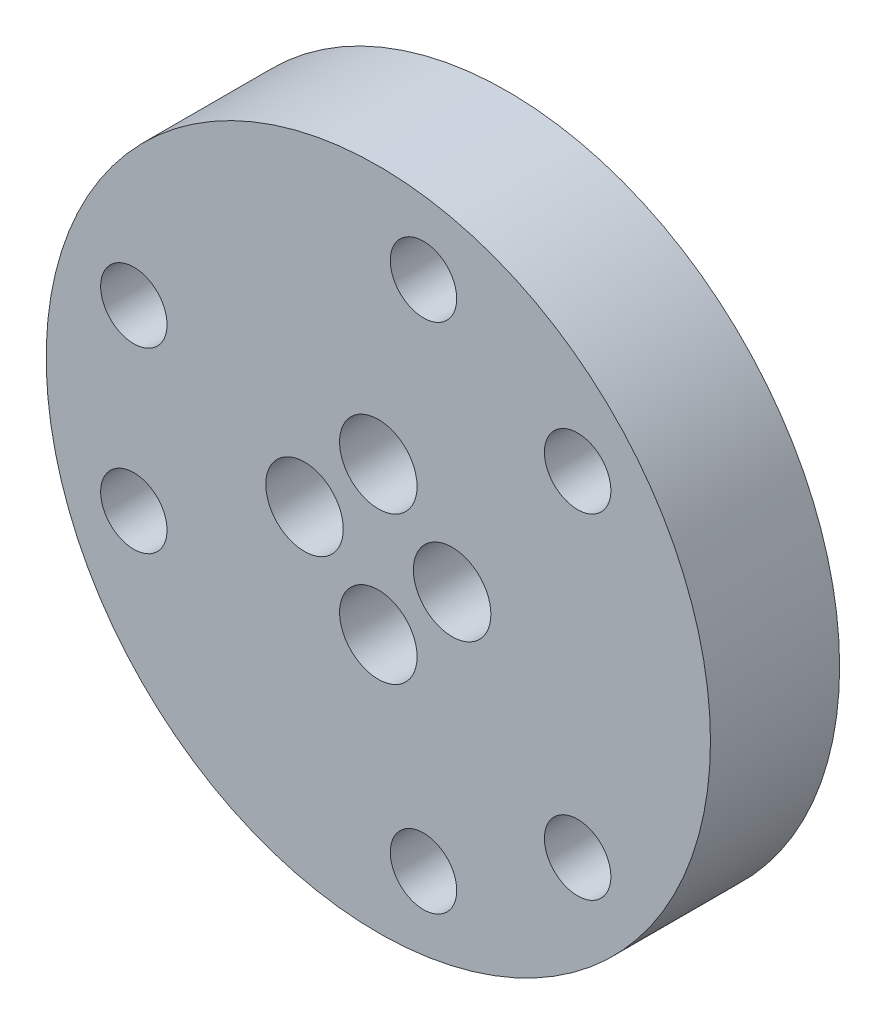
SolidWorks part; units mm, degrees
ref_plane "정면" through (0, 0, 0) normal (0, 0, 1) x (1, 0, 0)
ref_plane "윗면" through (0, 0, 0) normal (0, 1, 0) x (1, 0, 0)
ref_plane "우측면" through (0, 0, 0) normal (1, 0, 0) x (0, 0, -1)
sketch "스케치1" plane through (0, 0, 0) normal (0, 0, 1) x (1, 0, 0)
  line L0 (0, 0) -> (-14.1, 0) construction
  line L1 (0, 0) -> (-13.2497, 4.8225) construction
  circle A0 centre (0, 0) radius 18
  circle A1 centre (0, 4) radius 1.1
  circle A2 centre (4, 0) radius 1.1
  circle A3 centre (0, -4) radius 1.1
  circle A4 centre (-4, 0) radius 1.1
  circle A5 centre (0, 0) radius 14.1 construction
  circle A6 centre (-13.2497, 4.8225) radius 1.6
  circle A7 centre (-13.2497, -4.8225) radius 1.6
  circle A8 centre (10.8012, 9.0633) radius 1.6
  circle A9 centre (2.4484, 13.8858) radius 1.6
  circle A10 centre (2.4484, -13.8858) radius 1.6
  circle A11 centre (10.8012, -9.0633) radius 1.6
  point P14 (0, 0)
  point P28 (0, 0)
  dimension "D1" = 36
  dimension "D2" = 2.2
  dimension "D6" = 28.2
  dimension "D7" = 3.2
  dimension "D3" = 4
  dimension "D5" = 20
  dimension "D4" = 4
  dimension "D8" = 3
extrude "보스-돌출1" add sketch "스케치1" along normal blind 7
sketch "스케치5" plane through (0, 0, 7) normal (0, 0, 1) x (1, 0, 0)
  circle A0 centre (0, 4) radius 2.1
  circle A1 centre (0, -4) radius 2.1
  circle A2 centre (4, 0) radius 2.1
  circle A3 centre (-4, 0) radius 2.1
  dimension "D2" = 4.2
extrude "컷-돌출1" cut sketch "스케치5" against normal blind 5.6
hole_wizard "M3 접시 머리 나사용 카운터싱크2" positions "스케치6" profile "스케치7" countersink size "M3" standard "ISO" end condition through all
sketch "스케치6" plane through (0, 0, 0) normal (0, 0, -1) x (-1, 0, 0)
  point P0 (-2.4484, 13.8858)
  point P3 (13.2497, 4.8225)
  point P6 (13.2497, -4.8225)
  point P9 (-2.4484, -13.8858)
  point P12 (-10.8012, -9.0633)
  point P15 (-10.8012, 9.0633)
sketch "스케치7" plane through (2.4484, 13.8858, 0) normal (1, 0, 0) x (0, 1, 0)
  line L0 (0, 0) -> (0, 7)
  line L1 (0, 7) -> (1.8, 7)
  line L2 (1.8, 7) -> (1.8, 1.35)
  line L3 (1.8, 1.35) -> (3.15, 0)
  line L5 (3.15, 0) -> (0, 0)
  line L6 (-1.8, 1.35) -> (-3.15, 0) construction
  line L11 (0, -6.35) -> (0, 107.95) construction
  dimension "관통 구멍 지름" = 3.6
  dimension "관통 구멍 깊이" = 7
  dimension "표면 카운터싱크 지름" = 6.3
  dimension "표면 카운터싱크 각도" = 90
